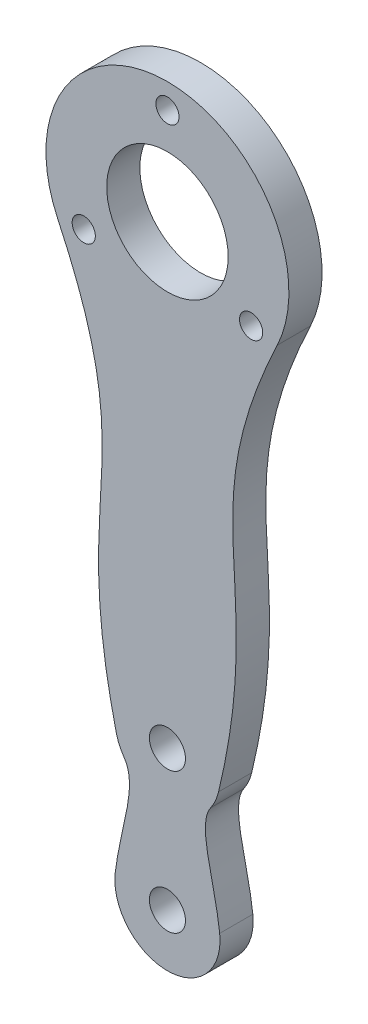
SolidWorks part; units mm, degrees
ref_plane "Front Plane" through (0, 0, 0) normal (0, 0, 1) x (1, 0, 0)
ref_plane "Top Plane" through (0, 0, 0) normal (0, 1, 0) x (1, 0, 0)
ref_plane "Right Plane" through (0, 0, 0) normal (1, 0, 0) x (0, 0, -1)
sketch "Sketch1" plane through (0, 0, 0) normal (0, 0, 1) x (1, 0, 0)
  line L0 (0, 25.4) -> (0, 47.4) construction
  line L1 (-7.5088, -10.1898) -> (27.3756, -83.9761) construction
  line L2 (-29.3599, 24.5212) -> (-19.8583, -15.1409) construction
  line L3 (5.0991, 45.4228) -> (7.0112, 62.0835) construction
  line L4 (-57.4285, 8.8239) -> (-63.3714, 17.3788) construction
  circle A0 centre (0, 25.4) radius 22
  circle A1 centre (0, -57.15) radius 3.2639
  circle A2 centre (0, -82.55) radius 3.2639
  circle A3 centre (0, 42.9) radius 2.1
  circle A4 centre (15.1554, 16.65) radius 2.1
  circle A5 centre (-15.1554, 16.65) radius 2.1
  circle A6 centre (0, 25.4) radius 22 construction
  circle A7 centre (0, -57.15) radius 3.2639 construction
  circle A8 centre (0, -82.55) radius 3.2639 construction
  circle A9 centre (0, -82.55) radius 9.525
  circle A10 centre (0, -57.15) radius 9.525
  circle A11 centre (0, 25.4) radius 11
  spline S0 degree 3 poles (-19.8892, 15.9969) (-3.9762, -17.6618) (-18.1477, -22.2816) (-9.2629, -59.3691) knots 0 0 0 0 1 1 1 1
  spline S1 degree 3 poles (19.8892, 15.9969) (3.9762, -17.6618) (18.1477, -22.2816) (9.2629, -59.3691) knots 0 0 0 0 1 1 1 1
  spline S2 degree 3 poles (-9.4629, -81.464) (-8.5613, -73.6078) (-5.2707, -66.2579) (-7.8227, -62.5843) knots 0 0 0 0 1 1 1 1
  spline S3 degree 3 poles (9.4629, -81.464) (8.5613, -73.6078) (5.2707, -66.2579) (7.8227, -62.5843) knots 0 0 0 0 1 1 1 1
  point P18 (0, 25.4)
  dimension "D3" = 19.05
  dimension "D4" = 4.2
  dimension "D5" = 22
  dimension "D2" = 17.5
  dimension "D1" = 3
extrude "Boss-Extrude1" add sketch "Sketch1" along normal blind 6 contours S1 A0 S0 A10 | A10 A1 | A9 S3 A10 S2 | A9 A2 | A0 A5 A4 A3
